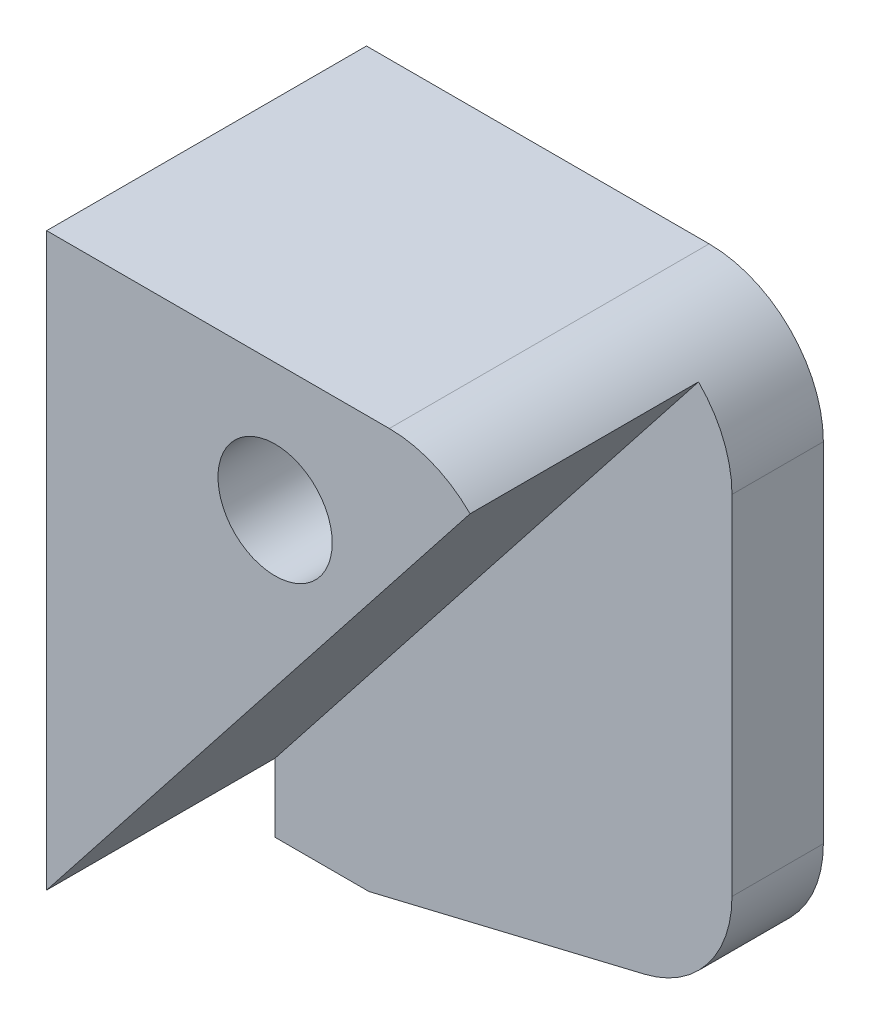
SolidWorks part; units mm, degrees
material "ﾊﾞﾙｻ"
ref_plane "正面" through (0, 0, 0) normal (0, 0, 1) x (1, 0, 0)
ref_plane "平面" through (0, 0, 0) normal (0, 1, 0) x (1, 0, 0)
ref_plane "右側面" through (0, 0, 0) normal (1, 0, 0) x (0, 0, -1)
sketch "ｽｹｯﾁ1" plane through (0, 0, 0) normal (0, 0, 1) x (1, 0, 0)
  line L0 (0, 0) -> (0, 15)
  line L1 (0, 15) -> (4, 15)
  line L2 (4, 15) -> (4, 22)
  line L3 (4, 22) -> (24, 22)
  line L4 (24, 22) -> (24, -6)
  line L5 (24, -6) -> (4, -6)
  line L6 (4, -6) -> (4, 0)
  line L7 (4, 0) -> (0, 0)
  line L8 (14, 22) -> (14, -6) construction
  line L9 (4, 22) -> (24, 8.3124) construction
  line L10 (8.1108, -6) -> (24, -2.1832)
  circle A0 centre (14, 16.41) radius 2.5
  dimension "D6" = 5
  dimension "D7" = 22.41
  dimension "D1" = 15
  dimension "D2" = 6
  dimension "D3" = 7
  dimension "D4" = 4
  dimension "D5" = 20
extrude "ﾎﾞｽ - 押し出し1" add sketch "ｽｹｯﾁ1" along normal blind 4 contours L5 L10 L4 L3 L2 L1 L0 L7 L6 A0
fillet "ﾌｨﾚｯﾄ1" radius 5 2 edges at (24, -2.1832, 2) (24, 22, 2)
sketch "ｽｹｯﾁ2" plane through (0, 0, 4) normal (0, 0, 1) x (1, 0, 0)
  line L0 (4, -6) -> (4, 0) construction
  line L1 (8.1108, -6) -> (4, -6) construction
  line L2 (8.1108, -6) -> (20.1678, -3.1038) construction
  line L3 (24, 17) -> (24, 1.7579) construction
  line L4 (4, 22) -> (19, 22) construction
  line L5 (4, 15) -> (4, 22) construction
  line L6 (4, -6) -> (4, 0)
  line L7 (8.1108, -6) -> (4, -6)
  line L8 (8.1108, -6) -> (20.1678, -3.1038)
  line L9 (24, 17) -> (24, 1.7579)
  line L10 (4, 22) -> (19, 22)
  line L11 (4, 15) -> (4, 22)
  line L12 (4, 15) -> (4, 0)
  line L13 (4, -3) -> (22.5355, 20.5355)
  arc A0 (20.1678, -3.1038) -> (24, 1.7579) centre (19, 1.7579) ccw construction
  arc A1 (24, 17) -> (19, 22) centre (19, 17) ccw construction
  arc A2 (20.1678, -3.1038) -> (24, 1.7579) centre (19, 1.7579) ccw
  arc A3 (24, 17) -> (19, 22) centre (19, 17) ccw
  circle M1 centre (14, 16.41) radius 2.5
  arc M5 (24, 17) -> (19, 22) centre (19, 17) ccw
  line M6 (19, 22) -> (4, 22)
  line M7 (4, 22) -> (4, 15)
  line M11 (4, 0) -> (4, -6)
extrude "ﾎﾞｽ - 押し出し2" add sketch "ｽｹｯﾁ2" along normal blind 10 contours L13 L12 M11 M5 M6 M7 M1
